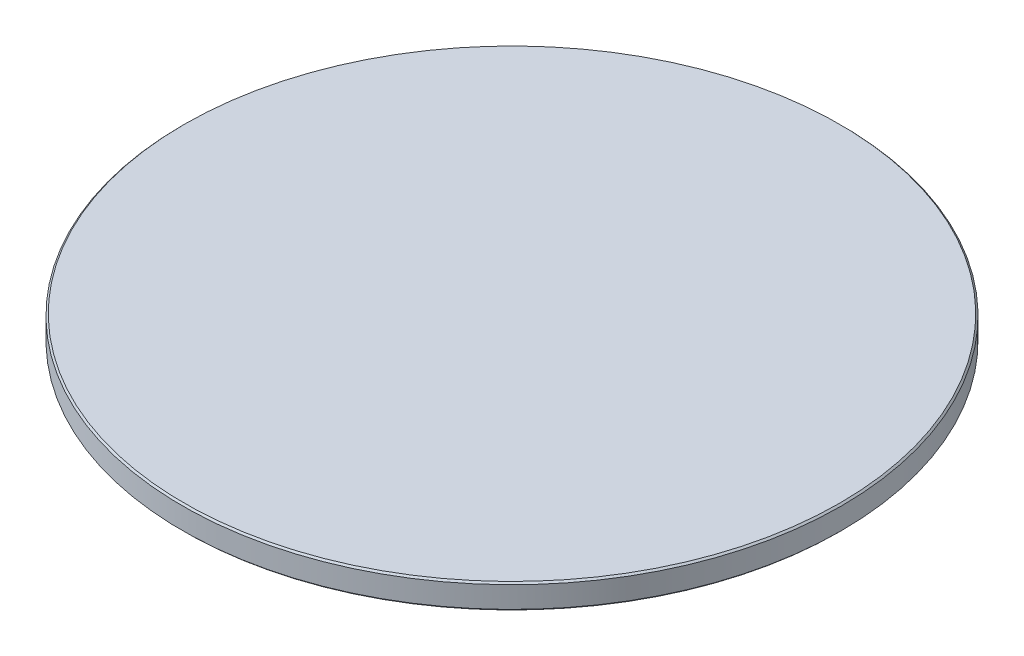
SolidWorks part; units mm, degrees
material "Borofloat"
ref_plane "Piano frontale" through (0, 0, 0) normal (0, 0, 1) x (1, 0, 0)
ref_plane "Piano superiore" through (0, 0, 0) normal (0, 1, 0) x (1, 0, 0)
ref_plane "Piano destro" through (0, 0, 0) normal (1, 0, 0) x (0, 0, -1)
sketch "Schizzo1" plane through (0, 0, 0) normal (0, 0, 1) x (1, 0, 0)
  line L0 (0, 3) -> (0, 0)
  line L1 (0, 3) -> (-39.8, 3)
  line L2 (0, 3) -> (0, 0) construction
  line L3 (0, 0) -> (-39.8, 0)
  line L4 (-40, 2.8) -> (-40, 0.2)
  line L5 (-39.8, 3) -> (-40, 2.8)
  line L6 (-40, 0.2) -> (-39.8, 0)
  point P1 (-40, 0)
  point P3 (-40, 3)
  dimension "D1" = 3
  dimension "D2" = 80
revolve "Rivoluzione1" add sketch "Schizzo1" angle 360 about L2
